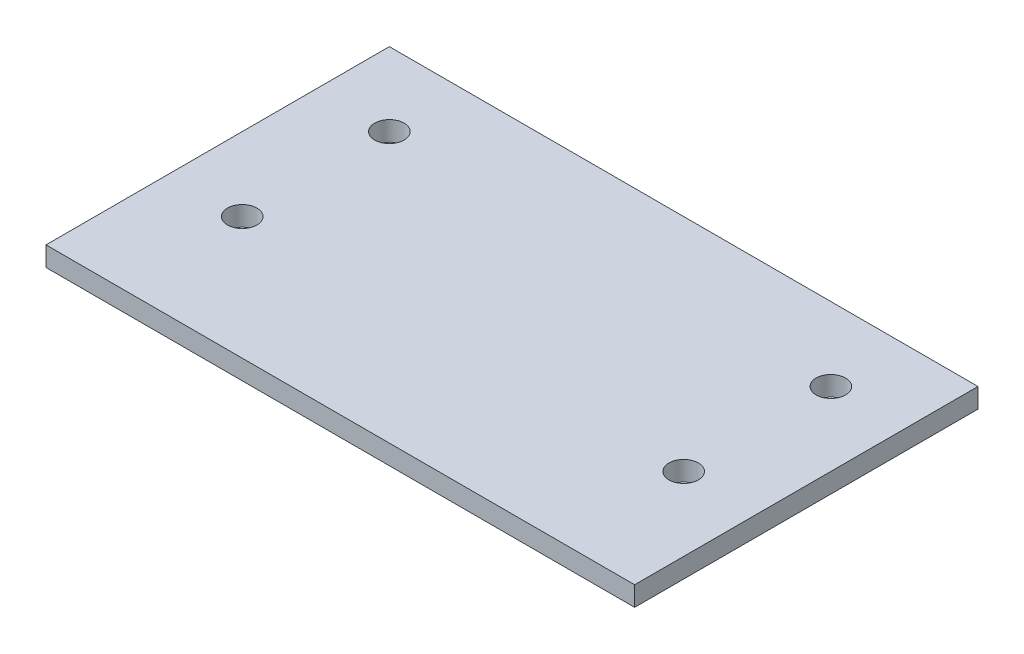
SolidWorks part; units mm, degrees
ref_plane "Alzado" through (0, 0, 0) normal (0, 0, 1) x (1, 0, 0)
ref_plane "Planta" through (0, 0, 0) normal (0, 1, 0) x (1, 0, 0)
ref_plane "Vista lateral" through (0, 0, 0) normal (1, 0, 0) x (0, 0, -1)
sketch "Croquis1" plane through (0, 0, 0) normal (0, 1, 0) x (1, 0, 0)
  line L1 (-30, -17.5) -> (30, -17.5)
  line L2 (-30, -17.5) -> (-30, 17.5)
  line L3 (-30, 17.5) -> (30, 17.5)
  line L4 (30, -17.5) -> (30, 17.5)
  line L5 (-30, -17.5) -> (30, 17.5) construction
  line L6 (-30, 17.5) -> (30, -17.5) construction
  point P0 (0, 0)
extrude "Saliente-Extruir1" add sketch "Croquis1" along normal blind 2
sketch "Croquis2" plane through (0, 0, 0) normal (0, -1, 0) x (1, 0, 0)
  circle A0 centre (22.5, -10) radius 1.5
  circle A1 centre (22.5, 5) radius 1.5
  circle A2 centre (-22.5, -10) radius 1.5
  circle A3 centre (-22.5, 5) radius 1.5
extrude "Cortar-Extruir1" cut sketch "Croquis2" against normal up to next
